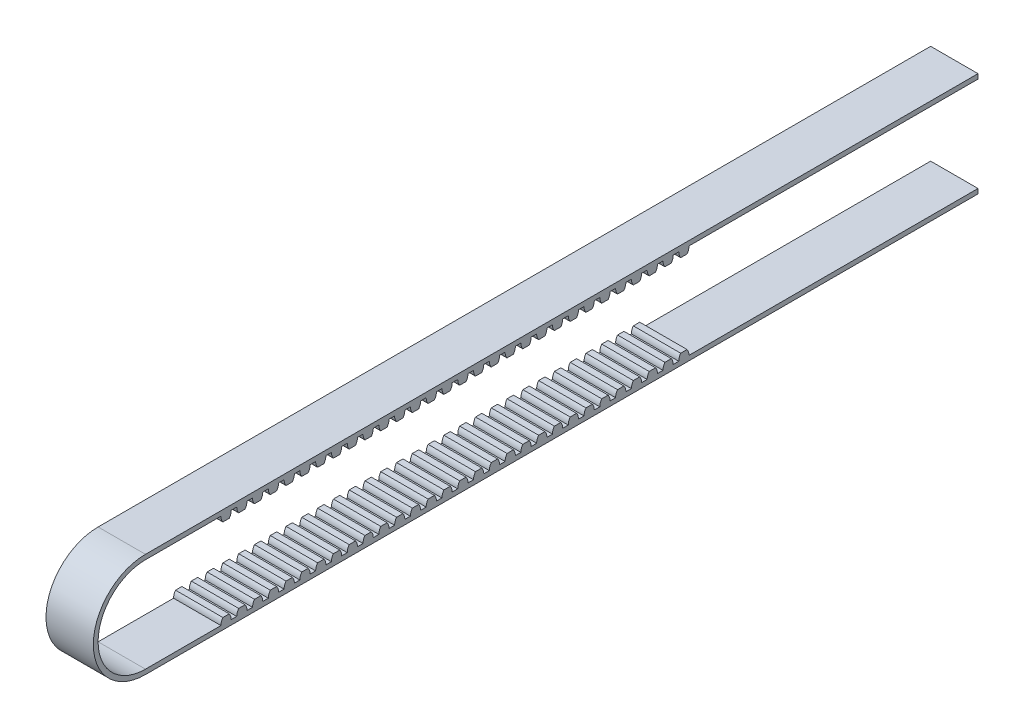
SolidWorks part; units mm, degrees
ref_plane "前视基准面" through (0, 0, 0) normal (0, 0, 1) x (1, 0, 0)
ref_plane "上视基准面" through (0, 0, 0) normal (0, 1, 0) x (1, 0, 0)
ref_plane "右视基准面" through (0, 0, 0) normal (1, 0, 0) x (0, 0, -1)
sketch "草图1" plane through (0, 0, 0) normal (0, 0, 1) x (1, 0, 0)
  line L1 (0, 0) -> (6, 0)
  line L2 (0, 0) -> (0, 0.6)
  line L3 (0, 0.6) -> (6, 0.6)
  line L4 (6, 0) -> (6, 0.6)
  dimension "D1" = 6
  dimension "D2" = 0.6
extrude "凸台-拉伸1" add sketch "草图1" along normal blind 100
sketch "草图2" plane through (6, 0, 0) normal (1, 0, 0) x (0, 0, -1)
  line L0 (-97.2141, -0.76) -> (-93.6093, -0.76) construction
  line L1 (-100, 0) -> (0, 0) construction
  line L2 (-95.9141, -0.76) -> (-95.9141, 1.3855) construction
  line L3 (-95.9141, 0) -> (-94.6141, 0) construction
  line L4 (-95.6688, -0.76) -> (-94.8594, -0.76)
  line L5 (-95.9141, 0) -> (-94.6141, 0)
  arc A0 (-95.2641, 1.1258) -> (-95.9141, 1.3) centre (-95.9141, 0) ccw
  arc A1 (-95.9141, 0) -> (-95.6688, -0.76) centre (-94.6141, 0) ccw
  arc A2 (-94.8594, -0.76) -> (-94.6141, 0) centre (-95.9141, 0) ccw
  line M7 (-100, 0) -> (0, 0)
  dimension "D1" = 0.76
  dimension "D2" = 1.3
extrude "凸台-拉伸2" add sketch "草图2" against normal blind 6 contours L4 A2 A1 M7
pattern_linear "阵列(线性)1" count 30 spacing 2 along (0, 0, -1) of "凸台-拉伸2"
sketch "草图3" plane through (6, 0, 0) normal (1, 0, 0) x (0, 0, -1)
  line L1 (-100, 0) -> (-105.4781, 0)
  line L2 (-100, 0) -> (-100, 0.6)
  line L3 (-100, 0.6) -> (-105.4781, 0.6)
  line L5 (-105.4781, -12) -> (-93.4434, -12)
  line L7 (-105.4781, -12.6) -> (-93.4434, -12.6)
  line L8 (-93.4434, -12) -> (-93.4434, -12.6)
  arc A0 (-105.4781, 0) -> (-105.4781, -12) centre (-105.4781, -6) ccw
  arc A1 (-105.4781, 0.6) -> (-105.4781, -12.6) centre (-105.4781, -6) ccw
  dimension "D1" = 6
extrude "凸台-拉伸3" add sketch "草图3" against normal blind 6
ref_plane "基准面1" through (0, -6, 0) normal (0, 1, 0) x (1, 0, 0)
mirror "镜向1" about plane through (0, -6, 0) normal (0, 1, 0) of "阵列(线性)1", "凸台-拉伸3", "凸台-拉伸1", "凸台-拉伸2"
